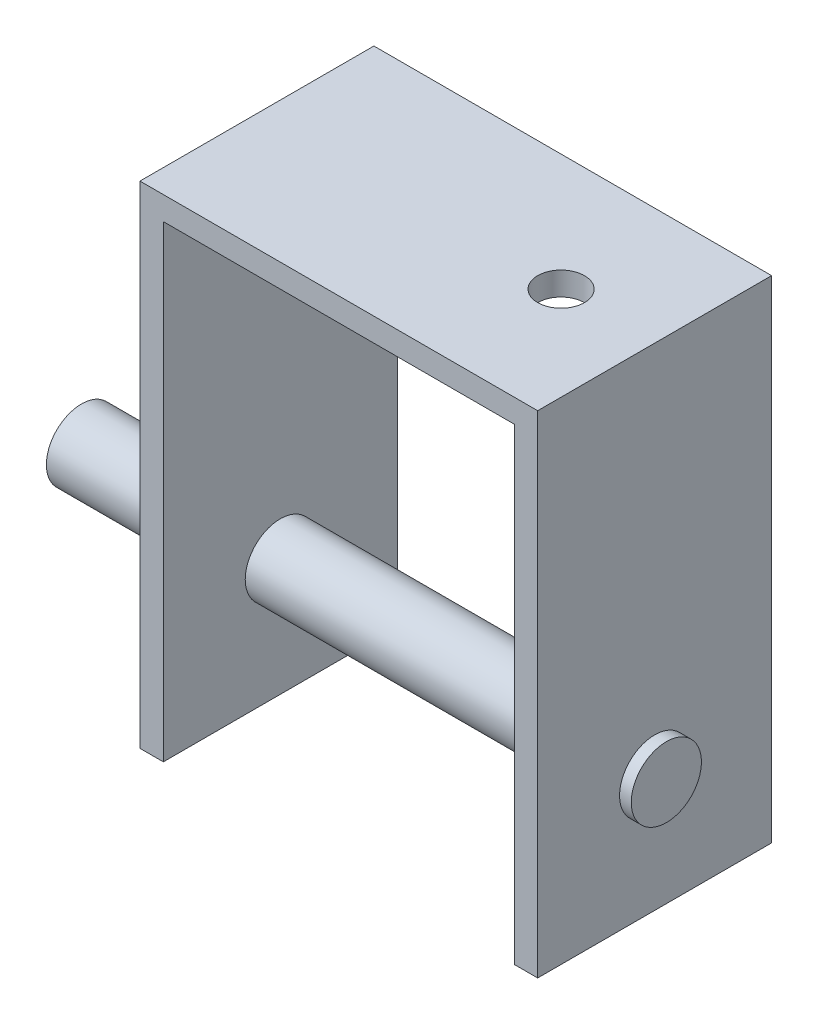
SolidWorks part; units mm, degrees
ref_plane "前视基准面" through (0, 0, 0) normal (0, 0, 1) x (1, 0, 0)
ref_plane "上视基准面" through (0, 0, 0) normal (0, 1, 0) x (1, 0, 0)
ref_plane "右视基准面" through (0, 0, 0) normal (1, 0, 0) x (0, 0, -1)
sketch "草图1" plane through (0, 0, 0) normal (0, 0, 1) x (1, 0, 0)
  line L0 (-38.9637, 28.8454) -> (-38.9637, -11.1546)
  line L1 (-38.9637, -11.1546) -> (-36.9637, -11.1546)
  line L2 (-36.9637, -11.1546) -> (-36.9637, 28.8454)
  line L3 (-36.9637, 28.8454) -> (-6.9637, 28.8454)
  line L4 (-6.9637, 28.8454) -> (-6.9637, -11.1546)
  line L5 (-6.9637, -11.1546) -> (-4.9637, -11.1546)
  line L6 (-4.9637, -11.1546) -> (-4.9637, 30.8454)
  line L7 (-4.9637, 30.8454) -> (-38.9637, 30.8454)
  line L8 (-38.9637, 30.8454) -> (-38.9637, 28.8454)
  dimension "D1" = 40
  dimension "D2" = 2
  dimension "D3" = 30
  dimension "D4" = 2
  dimension "D5" = 42
extrude "凸台-拉伸1" add sketch "草图1" along normal blind 20
sketch "草图3" plane through (-38.9637, 0, 0) normal (-1, 0, 0) x (0, 0, 1)
  line L0 (10, 30.8454) -> (10, -11.1546) construction
  line L1 (20, 30.8454) -> (0, 30.8454) construction
  line L2 (20, -11.1546) -> (0, -11.1546) construction
  line L3 (10, -11.1546) -> (10, -1.1546) construction
  circle A1 centre (10, -1.1546) radius 3
  dimension "D1" = 10
  dimension "D2" = 6
extrude "凸台-拉伸2" add sketch "草图3" along normal blind 15 and the other way blind 35
sketch "草图4" plane through (0, 30.8454, 0) normal (0, 1, 0) x (1, 0, 0)
  line L0 (-38.9637, -10) -> (-12.9637, -10) construction
  line L1 (-38.9637, -20) -> (-38.9637, 0) construction
  circle A0 centre (-12.9637, -10) radius 2
  dimension "D2" = 4
  dimension "D1" = 26
extrude "切除-拉伸1" cut sketch "草图4" against normal blind 2
